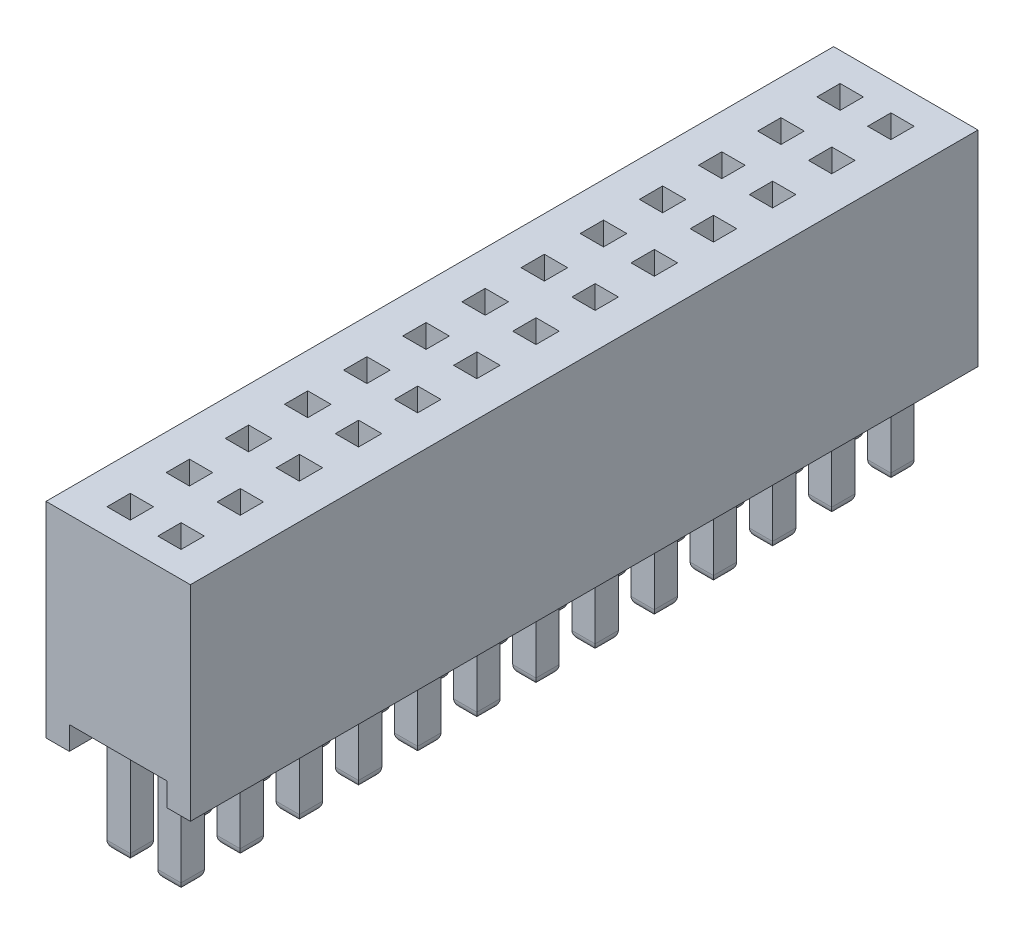
SolidWorks part; units mm, degrees
material "黄銅"
ref_plane "Front Plane" through (0, 0, 0) normal (0, 0, 1) x (1, 0, 0)
ref_plane "Top Plane" through (0, 0, 0) normal (0, 1, 0) x (1, 0, 0)
ref_plane "Right Plane" through (0, 0, 0) normal (1, 0, 0) x (0, 0, -1)
sketch "Sketch1" plane through (0, 0, 0) normal (0, 0, 1) x (1, 0, 0)
  line L0 (0.5, -4.4) -> (0.5, -3.9)
  line L1 (0, 0) -> (3.1, 0)
  line L2 (0, 0) -> (0, -4.4)
  line L3 (0, -4.4) -> (0.5, -4.4)
  line L4 (3.1, 0) -> (3.1, -4.4)
  line L5 (0.5, -3.9) -> (2.6, -3.9)
  line L6 (2.6, -3.9) -> (2.6, -4.4)
  line L7 (2.6, -4.4) -> (3.1, -4.4)
  dimension "D1" = 4.4
  dimension "D2" = 3.1
  dimension "D3" = 0.5
  dimension "D4" = 0.5
  dimension "D5" = 0.5
extrude "Boss-Extrude1" add sketch "Sketch1" along normal blind 16.91
sketch "Sketch4" plane through (0, 0, 0) normal (0, 1, 0) x (1, 0, 0)
  line L0 (0.755, -2.3856) -> (1.255, -2.3856)
  line L1 (0.755, -0.6156) -> (1.255, -0.6156)
  line L2 (0.755, -0.6156) -> (0.755, -1.1156)
  line L3 (0.755, -1.1156) -> (1.255, -1.1156)
  line L4 (1.255, -0.6156) -> (1.255, -1.1156)
  line L5 (1.8465, -2.3856) -> (2.345, -2.3856)
  line L6 (1.8465, -0.6156) -> (2.345, -0.6156)
  line L7 (1.8465, -0.6156) -> (1.8465, -1.1156)
  line L8 (1.8465, -1.1156) -> (2.345, -1.1156)
  line L9 (2.345, -0.6156) -> (2.345, -1.1156)
  line L10 (1.8465, -1.8856) -> (1.8465, -2.3856)
  line L11 (2.345, -1.8856) -> (2.345, -2.3856)
  line L12 (1.8465, -1.8856) -> (2.345, -1.8856)
  line L13 (1.255, -1.8856) -> (1.255, -2.3856)
  line L14 (0.755, -1.8856) -> (0.755, -2.3856)
  line L15 (0.755, -1.8856) -> (1.255, -1.8856)
  line L16 (0.755, -3.6556) -> (1.255, -3.6556)
  line L17 (1.8465, -3.6556) -> (2.345, -3.6556)
  line L18 (1.8465, -3.1556) -> (1.8465, -3.6556)
  line L19 (2.345, -3.1556) -> (2.345, -3.6556)
  line L20 (1.8465, -3.1556) -> (2.345, -3.1556)
  line L21 (1.255, -3.1556) -> (1.255, -3.6556)
  line L22 (0.755, -3.1556) -> (0.755, -3.6556)
  line L23 (0.755, -3.1556) -> (1.255, -3.1556)
  line L24 (0.755, -4.9256) -> (1.255, -4.9256)
  line L25 (1.8465, -4.9256) -> (2.345, -4.9256)
  line L26 (1.8465, -4.4256) -> (1.8465, -4.9256)
  line L27 (2.345, -4.4256) -> (2.345, -4.9256)
  line L28 (1.8465, -4.4256) -> (2.345, -4.4256)
  line L29 (1.255, -4.4256) -> (1.255, -4.9256)
  line L30 (0.755, -4.4256) -> (0.755, -4.9256)
  line L31 (0.755, -4.4256) -> (1.255, -4.4256)
  line L32 (0.755, -6.1956) -> (1.255, -6.1956)
  line L33 (1.8465, -6.1956) -> (2.345, -6.1956)
  line L34 (1.8465, -5.6956) -> (1.8465, -6.1956)
  line L35 (2.345, -5.6956) -> (2.345, -6.1956)
  line L36 (1.8465, -5.6956) -> (2.345, -5.6956)
  line L37 (1.255, -5.6956) -> (1.255, -6.1956)
  line L38 (0.755, -5.6956) -> (0.755, -6.1956)
  line L39 (0.755, -5.6956) -> (1.255, -5.6956)
  line L40 (0.755, -7.4656) -> (1.255, -7.4656)
  line L41 (1.8465, -7.4656) -> (2.345, -7.4656)
  line L42 (1.8465, -6.9656) -> (1.8465, -7.4656)
  line L43 (2.345, -6.9656) -> (2.345, -7.4656)
  line L44 (1.8465, -6.9656) -> (2.345, -6.9656)
  line L45 (1.255, -6.9656) -> (1.255, -7.4656)
  line L46 (0.755, -6.9656) -> (0.755, -7.4656)
  line L47 (0.755, -6.9656) -> (1.255, -6.9656)
  line L48 (0.755, -8.7356) -> (1.255, -8.7356)
  line L49 (1.8465, -8.7356) -> (2.345, -8.7356)
  line L50 (1.8465, -8.2356) -> (1.8465, -8.7356)
  line L51 (2.345, -8.2356) -> (2.345, -8.7356)
  line L52 (1.8465, -8.2356) -> (2.345, -8.2356)
  line L53 (1.255, -8.2356) -> (1.255, -8.7356)
  line L54 (0.755, -8.2356) -> (0.755, -8.7356)
  line L55 (0.755, -8.2356) -> (1.255, -8.2356)
  line L56 (0.755, -10.0056) -> (1.255, -10.0056)
  line L57 (1.8465, -10.0056) -> (2.345, -10.0056)
  line L58 (1.8465, -9.5056) -> (1.8465, -10.0056)
  line L59 (2.345, -9.5056) -> (2.345, -10.0056)
  line L60 (1.8465, -9.5056) -> (2.345, -9.5056)
  line L61 (1.255, -9.5056) -> (1.255, -10.0056)
  line L62 (0.755, -9.5056) -> (0.755, -10.0056)
  line L63 (0.755, -9.5056) -> (1.255, -9.5056)
  line L64 (0.755, -11.2756) -> (1.255, -11.2756)
  line L65 (1.8465, -11.2756) -> (2.345, -11.2756)
  line L66 (1.8465, -10.7756) -> (1.8465, -11.2756)
  line L67 (2.345, -10.7756) -> (2.345, -11.2756)
  line L68 (1.8465, -10.7756) -> (2.345, -10.7756)
  line L69 (1.255, -10.7756) -> (1.255, -11.2756)
  line L70 (0.755, -10.7756) -> (0.755, -11.2756)
  line L71 (0.755, -10.7756) -> (1.255, -10.7756)
  line L72 (0.755, -12.5456) -> (1.255, -12.5456)
  line L73 (1.8465, -12.5456) -> (2.345, -12.5456)
  line L74 (1.8465, -12.0456) -> (1.8465, -12.5456)
  line L75 (2.345, -12.0456) -> (2.345, -12.5456)
  line L76 (1.8465, -12.0456) -> (2.345, -12.0456)
  line L77 (1.255, -12.0456) -> (1.255, -12.5456)
  line L78 (0.755, -12.0456) -> (0.755, -12.5456)
  line L79 (0.755, -12.0456) -> (1.255, -12.0456)
  line L80 (0.755, -13.8156) -> (1.255, -13.8156)
  line L81 (1.8465, -13.8156) -> (2.345, -13.8156)
  line L82 (1.8465, -13.3156) -> (1.8465, -13.8156)
  line L83 (2.345, -13.3156) -> (2.345, -13.8156)
  line L84 (1.8465, -13.3156) -> (2.345, -13.3156)
  line L85 (1.255, -13.3156) -> (1.255, -13.8156)
  line L86 (0.755, -13.3156) -> (0.755, -13.8156)
  line L87 (0.755, -13.3156) -> (1.255, -13.3156)
  line L88 (0.755, -15.0856) -> (1.255, -15.0856)
  line L89 (1.8465, -15.0856) -> (2.345, -15.0856)
  line L90 (1.8465, -14.5856) -> (1.8465, -15.0856)
  line L91 (2.345, -14.5856) -> (2.345, -15.0856)
  line L92 (1.8465, -14.5856) -> (2.345, -14.5856)
  line L93 (1.255, -14.5856) -> (1.255, -15.0856)
  line L94 (0.755, -14.5856) -> (0.755, -15.0856)
  line L95 (0.755, -14.5856) -> (1.255, -14.5856)
  line L96 (0.755, -16.3556) -> (1.255, -16.3556)
  line L97 (1.8465, -16.3556) -> (2.345, -16.3556)
  line L98 (1.8465, -15.8556) -> (1.8465, -16.3556)
  line L99 (2.345, -15.8556) -> (2.345, -16.3556)
  line L100 (1.8465, -15.8556) -> (2.345, -15.8556)
  line L101 (1.255, -15.8556) -> (1.255, -16.3556)
  line L102 (0.755, -15.8556) -> (0.755, -16.3556)
  line L103 (0.755, -15.8556) -> (1.255, -15.8556)
  line L105 (3.1, -16.91) -> (3.1, 0) construction
  line L106 (0, -16.91) -> (0, 0) construction
  dimension "D1" = 0.5
  dimension "D2" = 0.5
  dimension "D3" = 13
  dimension "D4" = 0.755
  dimension "D5" = 0.755
extrude "Cut-Extrude4" cut sketch "Sketch4" against normal offset from surface (3.4 mm away) 0.5 up to face at (1.55, -3.9, 8.455)
sketch "Sketch5" plane through (0, -3.4, 0) normal (0, 1, 0) x (1, 0, 0)
  line L0 (1.8465, -2.3856) -> (2.345, -2.3856)
  line L1 (0.755, -0.6156) -> (1.255, -0.6156)
  line L2 (0.755, -0.6156) -> (0.755, -1.1156)
  line L3 (0.755, -1.1156) -> (1.255, -1.1156)
  line L4 (1.255, -0.6156) -> (1.255, -1.1156)
  line L5 (1.8465, -1.1156) -> (2.345, -1.1156)
  line L6 (1.8465, -1.1156) -> (1.8465, -0.6156)
  line L7 (1.8465, -0.6156) -> (2.345, -0.6156)
  line L8 (2.345, -1.1156) -> (2.345, -0.6156)
  line L9 (0.755, -2.3856) -> (1.255, -2.3856)
  line L10 (0.755, -1.8856) -> (1.255, -1.8856)
  line L11 (1.255, -1.8856) -> (1.255, -2.3856)
  line L12 (0.755, -1.8856) -> (0.755, -2.3856)
  line L13 (1.8465, -1.8856) -> (2.345, -1.8856)
  line L14 (2.345, -2.3856) -> (2.345, -1.8856)
  line L15 (1.8465, -2.3856) -> (1.8465, -1.8856)
  line L16 (1.8465, -3.6556) -> (2.345, -3.6556)
  line L17 (0.755, -3.6556) -> (1.255, -3.6556)
  line L18 (0.755, -3.1556) -> (1.255, -3.1556)
  line L19 (1.255, -3.1556) -> (1.255, -3.6556)
  line L20 (0.755, -3.1556) -> (0.755, -3.6556)
  line L21 (1.8465, -3.1556) -> (2.345, -3.1556)
  line L22 (2.345, -3.6556) -> (2.345, -3.1556)
  line L23 (1.8465, -3.6556) -> (1.8465, -3.1556)
  line L24 (1.8465, -4.9256) -> (2.345, -4.9256)
  line L25 (0.755, -4.9256) -> (1.255, -4.9256)
  line L26 (0.755, -4.4256) -> (1.255, -4.4256)
  line L27 (1.255, -4.4256) -> (1.255, -4.9256)
  line L28 (0.755, -4.4256) -> (0.755, -4.9256)
  line L29 (1.8465, -4.4256) -> (2.345, -4.4256)
  line L30 (2.345, -4.9256) -> (2.345, -4.4256)
  line L31 (1.8465, -4.9256) -> (1.8465, -4.4256)
  line L32 (1.8465, -6.1956) -> (2.345, -6.1956)
  line L33 (0.755, -6.1956) -> (1.255, -6.1956)
  line L34 (0.755, -5.6956) -> (1.255, -5.6956)
  line L35 (1.255, -5.6956) -> (1.255, -6.1956)
  line L36 (0.755, -5.6956) -> (0.755, -6.1956)
  line L37 (1.8465, -5.6956) -> (2.345, -5.6956)
  line L38 (2.345, -6.1956) -> (2.345, -5.6956)
  line L39 (1.8465, -6.1956) -> (1.8465, -5.6956)
  line L40 (1.8465, -7.4656) -> (2.345, -7.4656)
  line L41 (0.755, -7.4656) -> (1.255, -7.4656)
  line L42 (0.755, -6.9656) -> (1.255, -6.9656)
  line L43 (1.255, -6.9656) -> (1.255, -7.4656)
  line L44 (0.755, -6.9656) -> (0.755, -7.4656)
  line L45 (1.8465, -6.9656) -> (2.345, -6.9656)
  line L46 (2.345, -7.4656) -> (2.345, -6.9656)
  line L47 (1.8465, -7.4656) -> (1.8465, -6.9656)
  line L48 (1.8465, -8.7356) -> (2.345, -8.7356)
  line L49 (0.755, -8.7356) -> (1.255, -8.7356)
  line L50 (0.755, -8.2356) -> (1.255, -8.2356)
  line L51 (1.255, -8.2356) -> (1.255, -8.7356)
  line L52 (0.755, -8.2356) -> (0.755, -8.7356)
  line L53 (1.8465, -8.2356) -> (2.345, -8.2356)
  line L54 (2.345, -8.7356) -> (2.345, -8.2356)
  line L55 (1.8465, -8.7356) -> (1.8465, -8.2356)
  line L56 (1.8465, -10.0056) -> (2.345, -10.0056)
  line L57 (0.755, -10.0056) -> (1.255, -10.0056)
  line L58 (0.755, -9.5056) -> (1.255, -9.5056)
  line L59 (1.255, -9.5056) -> (1.255, -10.0056)
  line L60 (0.755, -9.5056) -> (0.755, -10.0056)
  line L61 (1.8465, -9.5056) -> (2.345, -9.5056)
  line L62 (2.345, -10.0056) -> (2.345, -9.5056)
  line L63 (1.8465, -10.0056) -> (1.8465, -9.5056)
  line L64 (1.8465, -11.2756) -> (2.345, -11.2756)
  line L65 (0.755, -11.2756) -> (1.255, -11.2756)
  line L66 (0.755, -10.7756) -> (1.255, -10.7756)
  line L67 (1.255, -10.7756) -> (1.255, -11.2756)
  line L68 (0.755, -10.7756) -> (0.755, -11.2756)
  line L69 (1.8465, -10.7756) -> (2.345, -10.7756)
  line L70 (2.345, -11.2756) -> (2.345, -10.7756)
  line L71 (1.8465, -11.2756) -> (1.8465, -10.7756)
  line L72 (1.8465, -12.5456) -> (2.345, -12.5456)
  line L73 (0.755, -12.5456) -> (1.255, -12.5456)
  line L74 (0.755, -12.0456) -> (1.255, -12.0456)
  line L75 (1.255, -12.0456) -> (1.255, -12.5456)
  line L76 (0.755, -12.0456) -> (0.755, -12.5456)
  line L77 (1.8465, -12.0456) -> (2.345, -12.0456)
  line L78 (2.345, -12.5456) -> (2.345, -12.0456)
  line L79 (1.8465, -12.5456) -> (1.8465, -12.0456)
  line L80 (1.8465, -13.8156) -> (2.345, -13.8156)
  line L81 (0.755, -13.8156) -> (1.255, -13.8156)
  line L82 (0.755, -13.3156) -> (1.255, -13.3156)
  line L83 (1.255, -13.3156) -> (1.255, -13.8156)
  line L84 (0.755, -13.3156) -> (0.755, -13.8156)
  line L85 (1.8465, -13.3156) -> (2.345, -13.3156)
  line L86 (2.345, -13.8156) -> (2.345, -13.3156)
  line L87 (1.8465, -13.8156) -> (1.8465, -13.3156)
  line L88 (1.8465, -15.0856) -> (2.345, -15.0856)
  line L89 (0.755, -15.0856) -> (1.255, -15.0856)
  line L90 (0.755, -14.5856) -> (1.255, -14.5856)
  line L91 (1.255, -14.5856) -> (1.255, -15.0856)
  line L92 (0.755, -14.5856) -> (0.755, -15.0856)
  line L93 (1.8465, -14.5856) -> (2.345, -14.5856)
  line L94 (2.345, -15.0856) -> (2.345, -14.5856)
  line L95 (1.8465, -15.0856) -> (1.8465, -14.5856)
  line L96 (1.8465, -16.3556) -> (2.345, -16.3556)
  line L97 (0.755, -16.3556) -> (1.255, -16.3556)
  line L98 (0.755, -15.8556) -> (1.255, -15.8556)
  line L99 (1.255, -15.8556) -> (1.255, -16.3556)
  line L100 (0.755, -15.8556) -> (0.755, -16.3556)
  line L101 (1.8465, -15.8556) -> (2.345, -15.8556)
  line L102 (2.345, -16.3556) -> (2.345, -15.8556)
  line L103 (1.8465, -16.3556) -> (1.8465, -15.8556)
  dimension "D1" = 13
extrude "Boss-Extrude3" add sketch "Sketch5" against normal blind 3
fillet "Fillet3" radius 0.2 104 edges at (2.0957, -6.4, 1.1156) (2.345, -6.4, 0.8656) (2.0957, -6.4, 0.6156) (1.8465, -6.4, 0.8656) (1.005, -6.4, 1.1156) (1.255, -6.4, 0.8656) (1.005, -6.4, 0.6156) (0.755, -6.4, 0.8656) (1.005, -6.4, 2.3856) (1.255, -6.4, 2.1356) (1.005, -6.4, 1.8856) (0.755, -6.4, 2.1356) (2.0957, -6.4, 2.3856) (2.345, -6.4, 2.1356) (2.0957, -6.4, 1.8856) (1.8465, -6.4, 2.1356) (2.0957, -6.4, 3.6556) (2.345, -6.4, 3.4056) (2.0957, -6.4, 3.1556) (1.8465, -6.4, 3.4056) (1.005, -6.4, 3.6556) (1.255, -6.4, 3.4056) (1.005, -6.4, 3.1556) (0.755, -6.4, 3.4056) (1.005, -6.4, 4.9256) (1.255, -6.4, 4.6756) (1.005, -6.4, 4.4256) (0.755, -6.4, 4.6756) (2.0957, -6.4, 4.9256) (2.345, -6.4, 4.6756) (2.0957, -6.4, 4.4256) (1.8465, -6.4, 4.6756) (2.0957, -6.4, 6.1956) (2.345, -6.4, 5.9456) (2.0957, -6.4, 5.6956) (1.8465, -6.4, 5.9456) (1.005, -6.4, 6.1956) (1.255, -6.4, 5.9456) (1.005, -6.4, 5.6956) (0.755, -6.4, 5.9456) (1.005, -6.4, 7.4656) (1.255, -6.4, 7.2156) (1.005, -6.4, 6.9656) (0.755, -6.4, 7.2156) (2.0957, -6.4, 7.4656) (2.345, -6.4, 7.2156) (2.0957, -6.4, 6.9656) (1.8465, -6.4, 7.2156) (2.0957, -6.4, 8.7356) (2.345, -6.4, 8.4856) (2.0957, -6.4, 8.2356) (1.8465, -6.4, 8.4856) (1.005, -6.4, 8.7356) (1.255, -6.4, 8.4856) (1.005, -6.4, 8.2356) (0.755, -6.4, 8.4856) (1.005, -6.4, 10.0056) (1.255, -6.4, 9.7556) (1.005, -6.4, 9.5056) (0.755, -6.4, 9.7556) (2.0957, -6.4, 10.0056) (2.345, -6.4, 9.7556) (2.0957, -6.4, 9.5056) (1.8465, -6.4, 9.7556) (2.0957, -6.4, 11.2756) (2.345, -6.4, 11.0256) (2.0957, -6.4, 10.7756) (1.8465, -6.4, 11.0256) (1.005, -6.4, 11.2756) (1.255, -6.4, 11.0256) (1.005, -6.4, 10.7756) (0.755, -6.4, 11.0256) (1.005, -6.4, 12.5456) (1.255, -6.4, 12.2956) (1.005, -6.4, 12.0456) (0.755, -6.4, 12.2956) (2.0957, -6.4, 12.5456) (2.345, -6.4, 12.2956) (2.0957, -6.4, 12.0456) (1.8465, -6.4, 12.2956) (2.0957, -6.4, 13.8156) (2.345, -6.4, 13.5656) (2.0957, -6.4, 13.3156) (1.8465, -6.4, 13.5656) (1.005, -6.4, 13.8156) (1.255, -6.4, 13.5656) (1.005, -6.4, 13.3156) (0.755, -6.4, 13.5656) (1.005, -6.4, 15.0856) (1.255, -6.4, 14.8356) (1.005, -6.4, 14.5856) (0.755, -6.4, 14.8356) (2.0957, -6.4, 15.0856) (2.345, -6.4, 14.8356) (2.0957, -6.4, 14.5856) (1.8465, -6.4, 14.8356) (2.0957, -6.4, 16.3556) (2.345, -6.4, 16.1056) (2.0957, -6.4, 15.8556) (1.8465, -6.4, 16.1056) (1.005, -6.4, 16.3556) (1.255, -6.4, 16.1056) (1.005, -6.4, 15.8556) (0.755, -6.4, 16.1056)
